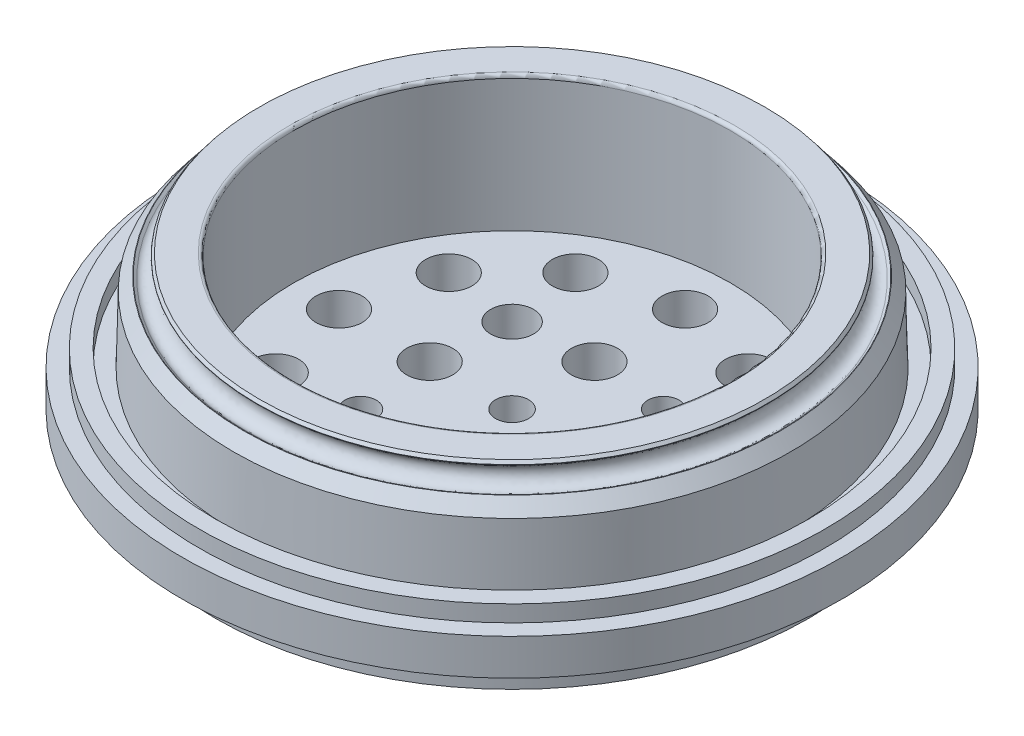
SolidWorks part; units mm, degrees
ref_plane "Front Plane" through (0, 0, 0) normal (0, 0, 1) x (1, 0, 0)
ref_plane "Top Plane" through (0, 0, 0) normal (0, 1, 0) x (1, 0, 0)
ref_plane "Right Plane" through (0, 0, 0) normal (1, 0, 0) x (0, 0, -1)
sketch "Sketch1" plane through (0, 0, 0) normal (0, 0, 1) x (1, 0, 0)
  line L0 (0, 0) -> (0, 38.71) construction
  line L2 (66.3265, 40.7481) -> (76.75, 40.7481)
  line L3 (76.75, 40.7481) -> (77.4739, 39.8142)
  line L5 (84.99, 10.7376) -> (89.9, 10.7376)
  line L6 (89.9, 10.7376) -> (89.9, 15.7376)
  line L7 (89.9, 15.7376) -> (95, 15.7376)
  line L8 (95, 15.7376) -> (95, 10.7376)
  line L9 (95, 10.7376) -> (100, 10.7376)
  line L10 (100, 10.7376) -> (100, -0.2624)
  line L24 (84.99, 30.5258) -> (84.99, 10.7376) construction
  line L27 (66.3265, -0.2624) -> (100, -0.2624)
  line L29 (84.5, 30.7497) -> (84.99, 10.7376)
  line L30 (66.3265, 40.7481) -> (66.3265, -0.2624)
  line L32 (78.5765, 38.3918) -> (78.5765, 27.8011) construction
  line L33 (80.5216, 34.1423) -> (81.3641, 34.7954)
  line L34 (76.6313, 39.1611) -> (77.4739, 39.8142)
  line L35 (81.3641, 34.7954) -> (84.5, 30.7497)
  line L36 (77.635, 39.6063) -> (81.203, 35.0032)
  circle A0 centre (78.5765, 36.6517) radius 2.665 construction
  circle A1 centre (78.55, 24.685) radius 2.665 construction
  ellipse E0 centre (78.5765, 36.6517) end of major axis (76.6313, 39.1611) minor radius 2.675
  dimension "D17" = 5.33
  dimension "D18" = 41.0105
  dimension "D16" = 66.3265
  dimension "D3" = 5.33
  dimension "D1" = 100
  dimension "D4" = 84.99
  dimension "D5" = 89.9
  dimension "D6" = 5.1
  dimension "D7" = 38.71
  dimension "D8" = 11
  dimension "D9" = 40.7481
  dimension "D10" = 5
  dimension "D11" = 37.78
  dimension "D12" = 84.5
  dimension "D13" = 12.25
  dimension "D14" = 1.066
  dimension "D15" = 76.75
  dimension "D19" = 3.175
  dimension "D20" = 2.675
  dimension "D21" = 78.55
revolve "Revolve1" add sketch "Sketch1" angle 360 about L0
fillet "Fillet1" radius 1 1 edges at (0, 40.7481, -66.3265)
sketch "Sketch2" plane through (0, -0.2624, 0) normal (0, -1, 0) x (1, 0, 0)
  line L0 (0, 0) -> (52.5, 0) construction
  line L2 (22.981, 22.981) -> (0, 0) construction
  line L3 (0, 0) -> (-22.981, -22.981) construction
  line L5 (-22.981, 22.981) -> (22.981, -22.981) construction
  circle A0 centre (0, 0) radius 52.5 construction
  circle A1 centre (0, 52.5) radius 12.5 construction
  circle A2 centre (0, 0) radius 10 construction
  circle A3 centre (0, 0) radius 25 construction
  circle A4 centre (0, 25) radius 12.5 construction
  circle A5 centre (0, 52.5) radius 7
  circle A6 centre (0, 25) radius 7
  circle A7 centre (0, 0) radius 5
  circle A8 centre (26.25, 45.4663) radius 7
  circle A9 centre (26.25, 45.4663) radius 12.5 construction
  circle A10 centre (45.4663, 26.25) radius 7
  circle A11 centre (45.4663, 26.25) radius 12.5 construction
  circle A12 centre (52.5, 0) radius 7
  circle A13 centre (52.5, 0) radius 12.5 construction
  circle A14 centre (45.4663, -26.25) radius 7
  circle A15 centre (45.4663, -26.25) radius 12.5 construction
  circle A16 centre (26.25, -45.4663) radius 7
  circle A17 centre (26.25, -45.4663) radius 12.5 construction
  circle A18 centre (0, -52.5) radius 7
  circle A19 centre (0, -52.5) radius 12.5 construction
  circle A20 centre (-26.25, -45.4663) radius 7
  circle A21 centre (-26.25, -45.4663) radius 12.5 construction
  circle A22 centre (-45.4663, -26.25) radius 7
  circle A23 centre (-45.4663, -26.25) radius 12.5 construction
  circle A24 centre (-52.5, 0) radius 7
  circle A25 centre (-52.5, 0) radius 12.5 construction
  circle A26 centre (-45.4663, 26.25) radius 7
  circle A27 centre (-45.4663, 26.25) radius 12.5 construction
  circle A28 centre (-26.25, 45.4663) radius 7
  circle A29 centre (-26.25, 45.4663) radius 12.5 construction
  circle A30 centre (25, 0) radius 12.5 construction
  circle A31 centre (25, 0) radius 7
  circle A32 centre (0, -25) radius 12.5 construction
  circle A33 centre (0, -25) radius 7
  circle A34 centre (-25, 0) radius 12.5 construction
  circle A35 centre (-25, 0) radius 7
  circle A36 centre (0, 0) radius 32.5 construction
  circle A37 centre (22.981, 22.981) radius 9.5 construction
  circle A38 centre (22.981, 22.981) radius 6.5
  circle A39 centre (-22.981, -22.981) radius 9.5 construction
  circle A40 centre (-22.981, -22.981) radius 6.5
  circle A41 centre (-22.981, 22.981) radius 4.7625
  circle A42 centre (22.981, -22.981) radius 4.7625
  circle A43 centre (-22.981, 22.981) radius 8.5 construction
  circle A44 centre (22.981, -22.981) radius 8.5 construction
  point P47 (0, 0)
  point P57 (0, 0)
  dimension "D1" = 105
  dimension "D2" = 25
  dimension "D3" = 20
  dimension "D4" = 65
  dimension "D5" = 50
  dimension "D6" = 10
  dimension "D7" = 19
  dimension "D8" = 14
  dimension "D12" = 13
  dimension "D15" = 9.525
  dimension "D16" = 17
  dimension "D11" = 45
  dimension "D13" = 90
  dimension "D14" = 180
  dimension "D9" = 12
  dimension "D10" = 4
sketch "Sketch3" plane through (0, -0.2624, 0) normal (0, -1, 0) x (1, 0, 0)
  circle A0 centre (0, 0) radius 90
  dimension "D1" = 180
extrude "Boss-Extrude1" add sketch "Sketch3" along normal blind 10
extrude "Cut-Extrude1" cut sketch "Sketch2" along normal blind 10
fillet "Fillet2" radius 0.1 2 edges at (0, 34.7954, -81.3641) (0, 39.8142, -77.4739)
